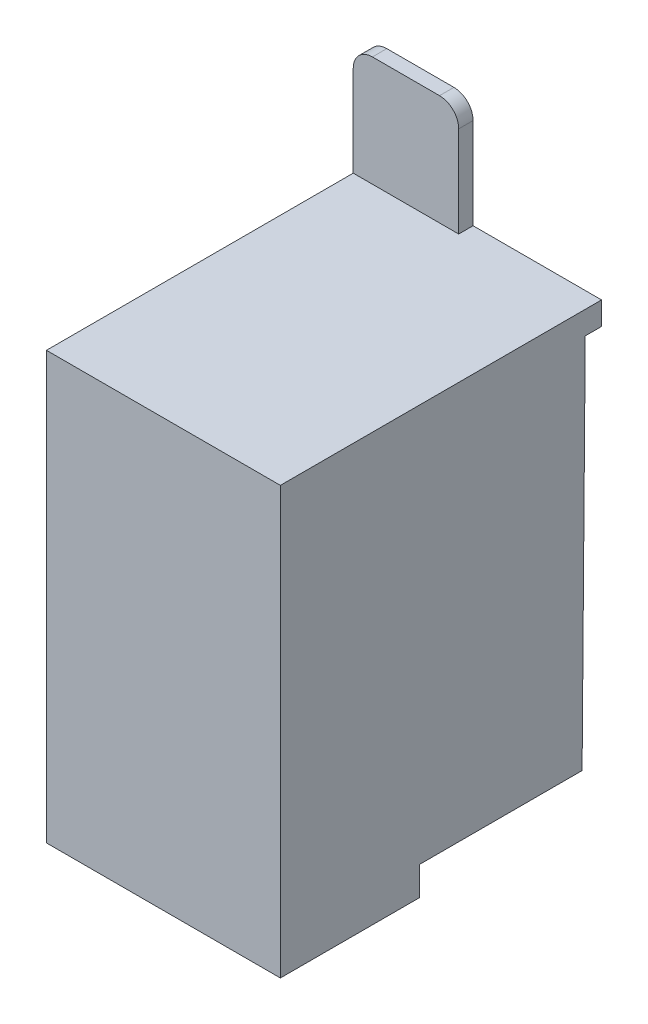
SolidWorks part; units mm, degrees
material "CA"
ref_plane "Front Plane" through (0, 0, 0) normal (0, 0, 1) x (1, 0, 0)
ref_plane "Top Plane" through (0, 0, 0) normal (0, 1, 0) x (1, 0, 0)
ref_plane "Right Plane" through (0, 0, 0) normal (1, 0, 0) x (0, 0, -1)
sketch "Sketch1" plane through (0, 0, 0) normal (0, 1, 0) x (1, 0, 0)
  line L1 (0, 0) -> (24.4, 0)
  line L2 (0, 0) -> (0, 33.5)
  line L3 (0, 33.5) -> (24.4, 33.5)
  line L4 (24.4, 0) -> (24.4, 33.5)
  dimension "D1" = 24.4
  dimension "D2" = 33.5
extrude "Boss-Extrude1" add sketch "Sketch1" along normal blind 41.5
sketch "Sketch3" plane through (0, 0, 0) normal (0, -1, 0) x (1, 0, 0)
  line L0 (24.4, 0) -> (24.4, -33.5) construction
  line L1 (0, 0) -> (24.4, 0)
  line L2 (0, 0) -> (0, -14.5)
  line L3 (0, -14.5) -> (6.45, -14.5)
  line L4 (24.4, 0) -> (24.4, -14.5)
  line L5 (6.45, -14.5) -> (6.45, -27.5)
  line L6 (6.45, -27.5) -> (17.95, -27.5)
  line L7 (17.95, -27.5) -> (17.95, -14.5)
  line L8 (17.95, -14.5) -> (24.4, -14.5)
  dimension "D1" = 14.5
  dimension "D2" = 11.5
  dimension "D3" = 13
extrude "Boss-Extrude2" add sketch "Sketch3" along normal blind 3
sketch "Sketch4" plane through (0, 41.5, 0) normal (0, 1, 0) x (-1, 0, 0)
  line L1 (-11, -32) -> (0, -32)
  line L2 (-11, -32) -> (-11, -33.5)
  line L3 (-11, -33.5) -> (0, -33.5)
  line L4 (0, -32) -> (0, -33.5)
  dimension "D1" = 11
  dimension "D2" = 1.5
extrude "Boss-Extrude3" add sketch "Sketch4" along normal blind 11.5
sketch "Sketch5" plane through (24.4, 0, 0) normal (1, 0, 0) x (0, 0, -1)
  line L0 (33.5, 0) -> (31.4694, 0)
  line L2 (14.5, 0) -> (33.5, 0) construction
  line L4 (31.4694, 0) -> (31.7979, 39.1006)
  line L5 (31.7979, 39.1006) -> (33.5, 39.1006)
  line L6 (33.5, 41.5) -> (33.5, 0) construction
  line L7 (33.5, 39.1006) -> (33.5, 0)
extrude "Cut-Extrude1" cut sketch "Sketch5" against normal through all
fillet "Fillet1" radius 2 2 edges at (0, 53, -32.75) (11, 53, -32.75)
